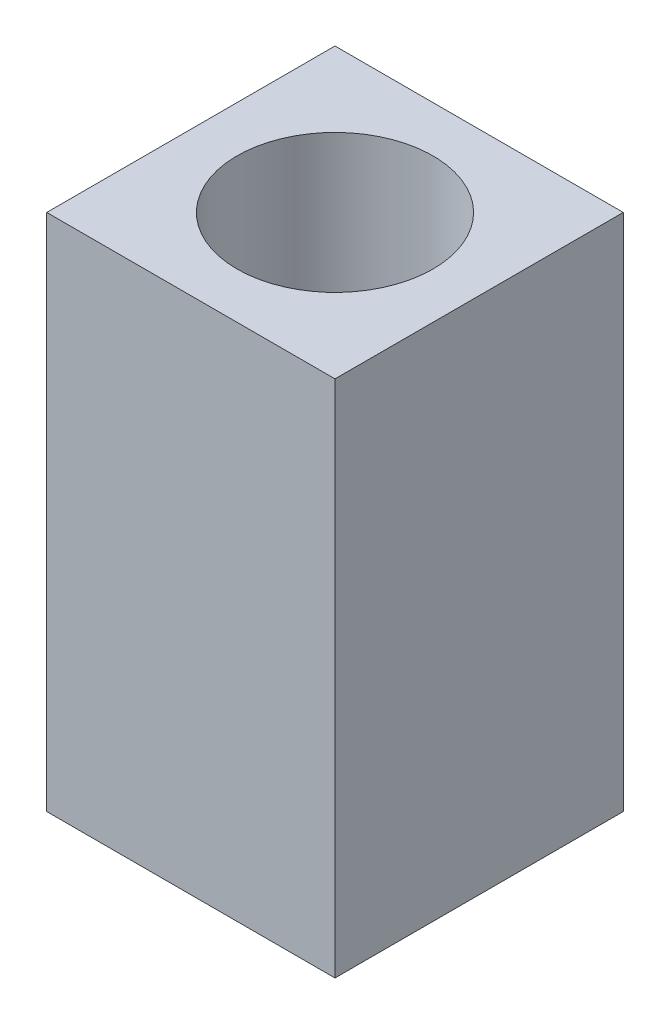
SolidWorks part; units mm, degrees
ref_plane "Front Plane" through (0, 0, 0) normal (0, 0, 1) x (1, 0, 0)
ref_plane "Top Plane" through (0, 0, 0) normal (0, 1, 0) x (1, 0, 0)
ref_plane "Right Plane" through (0, 0, 0) normal (1, 0, 0) x (0, 0, -1)
sketch "Sketch1" plane through (0, 0, 0) normal (0, 1, 0) x (1, 0, 0)
  line L1 (-2.5, -2.5) -> (2.5, -2.5)
  line L2 (-2.5, -2.5) -> (-2.5, 2.5)
  line L3 (-2.5, 2.5) -> (2.5, 2.5)
  line L4 (2.5, -2.5) -> (2.5, 2.5)
  line L5 (-2.5, -2.5) -> (2.5, 2.5) construction
  line L6 (-2.5, 2.5) -> (2.5, -2.5) construction
  circle A0 centre (0, 0) radius 1.7
  dimension "D1" = 3.4
  dimension "D2" = 5
extrude "Boss-Extrude1" add sketch "Sketch1" along normal blind 9
